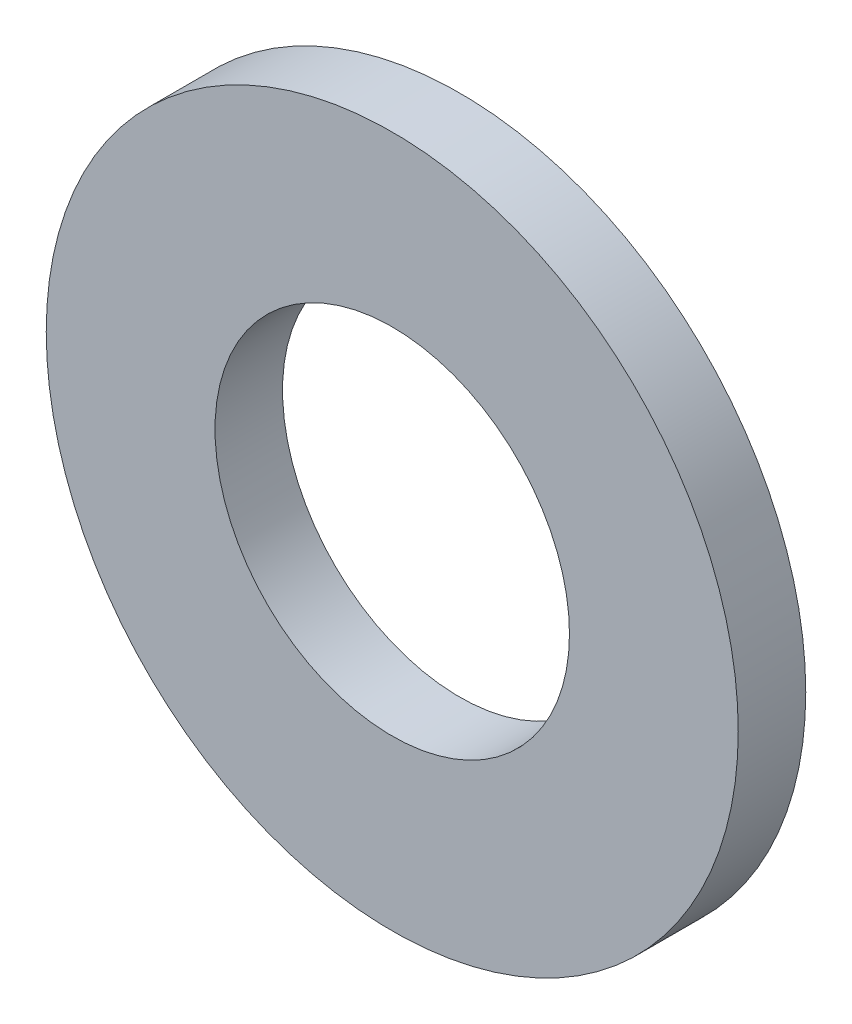
SolidWorks part; units mm, degrees
ref_plane "Front Plane" through (0, 0, 0) normal (0, 0, 1) x (1, 0, 0)
ref_plane "Top Plane" through (0, 0, 0) normal (0, 1, 0) x (1, 0, 0)
ref_plane "Right Plane" through (0, 0, 0) normal (1, 0, 0) x (0, 0, -1)
sketch "Sketch2" plane through (0, 0, 0) normal (0, 0, 1) x (1, 0, 0)
  circle A0 centre (0, 0) radius 3.15
  circle A1 centre (0, 0) radius 6.15
  dimension "D1" = 6.3
  dimension "D2" = 3
extrude "Boss-Extrude1" add sketch "Sketch2" along normal blind 1.2
